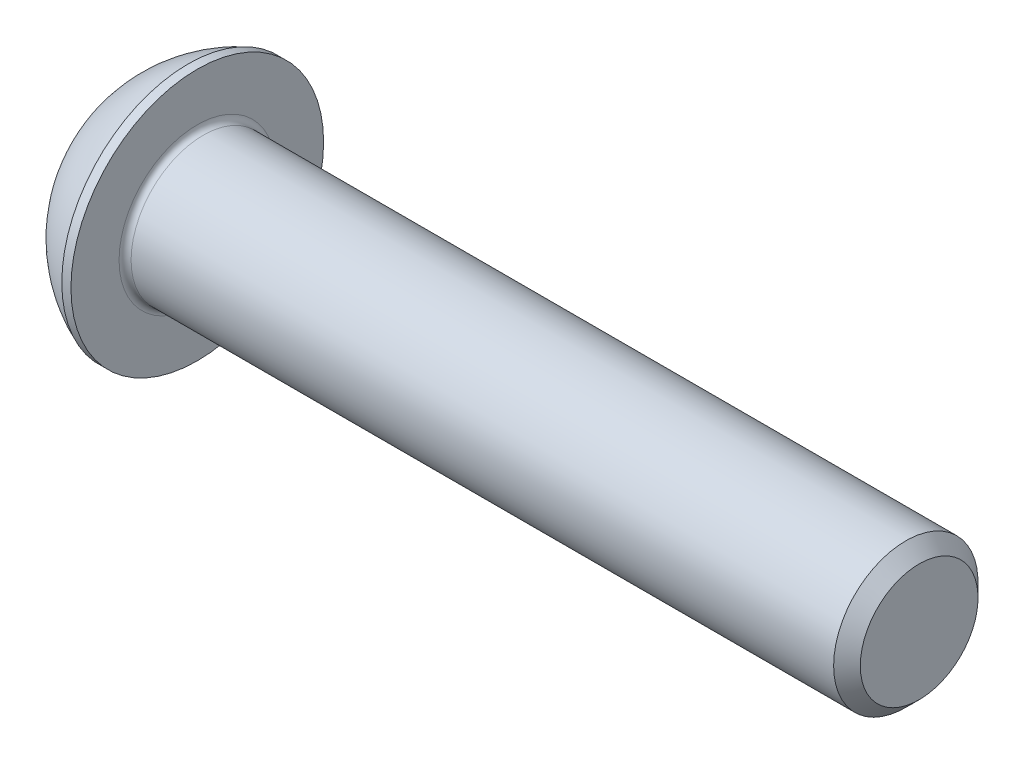
SolidWorks part; units mm, degrees
ref_plane "Plane1" through (0, 0, 0) normal (0, 0, 1) x (1, 0, 0)
ref_plane "Plane2" through (0, 0, 0) normal (0, 1, 0) x (1, 0, 0)
ref_plane "Plane3" through (0, 0, 0) normal (1, 0, 0) x (0, 0, -1)
sketch "BodySke" plane through (0, 0, 0) normal (0, 0, 1) x (1, 0, 0)
  line L0 (33.3, 0) -> (33.3, 2.4455)
  line L1 (32.7455, 3) -> (3.3, 3)
  line L2 (3.3, 3) -> (3.3, 5.25)
  line L3 (3.3, 5.25) -> (2.92, 5.25)
  line L4 (0, 0) -> (101.6, 0) construction
  line L5 (3.3, -5.25) -> (2.92, -5.25) construction
  line L6 (55.6768, -3) -> (3.3, -3) construction
  line L7 (33.3, 0) -> (0, 0)
  line L8 (0, 2.625) -> (0, -2.625) construction
  line L9 (0, 0) -> (0, 2.625)
  line L10 (33.3, 2.4455) -> (32.7455, 3)
  line L11 (33.3, -2.4455) -> (32.7455, -3) construction
  line L12 (4.3, 9.525) -> (4.3, -3) construction
  line L13 (3.3, 9.525) -> (3.3, -3) construction
  arc A1 (0, 2.625) -> (2.92, 5.25) centre (4.9997, 0) cw
  dimension "Head_side_ht" = 0.38
  dimension "Body_ch_ang" = 45
revolve "BaseBody" add sketch "BodySke" angle 360 about L4
cosmetic thread "ThreadCosmetic" [suppressed] parameters "Thread_length"=28, "Thread_minor"=4.891
fillet "Fillet1" radius 0.25 1 edges at (3.3, 0, 3)
sketch "Sketch2" plane through (0, 0, 0) normal (0, 0, 1) x (1, 0, 0)
  line L0 (0, 2) -> (2.08, 2)
  line L1 (2.08, 2) -> (3.2347, 0)
  line L3 (3.2347, 0) -> (0, 0)
  line L4 (0, 0) -> (0, 2)
  line L5 (0, -2) -> (2.08, -2) construction
  line L6 (0, 0) -> (47.625, 0) construction
  dimension "D2" = 60
  dimension "PreBroach_depth" = 2.08
  dimension "PreBroach_dia" = 4
revolve "PreBroach" cut sketch "Sketch2" angle 360 about L6
sketch "Sketch3" plane through (0, 0, 0) normal (1, 0, 0) x (0, 0, -1)
  line L0 (-2, -1.1547) -> (-2, 1.1547)
  line L1 (-2, 1.1547) -> (0, 2.3094)
  line L2 (0, 2.3094) -> (2, 1.1547)
  line L3 (2, 1.1547) -> (2, -1.1547)
  line L4 (2, -1.1547) -> (0, -2.3094)
  line L5 (0, -2.3094) -> (-2, -1.1547)
extrude "Hex" cut sketch "Sketch3" along normal blind 2.08
sketch "ThdSchSke" plane through (0, 0, 0) normal (0, 0, 1) x (1, 0, 0)
  line L0 (5.3, -2.4455) -> (4.9117, -3)
  line L1 (5.3, -2.4455) -> (5.6883, -3)
  line L2 (5.6883, -3) -> (5.6883, -3.75)
  line L3 (-3.175, 0) -> (5.1513, 0) construction
  line L5 (5.6883, -3.75) -> (4.9117, -3.75)
  line L6 (4.9117, -3.75) -> (4.9117, -3)
  dimension "SideAngle" = 55
  dimension "VeeAngle" = 70
revolve "ThreadSchematic" [suppressed] cut sketch "ThdSchSke" angle 360 about L3
pattern_linear "ThdSchPat" [suppressed]
equation "\"D1@BodySke\" = \"Head_dia@BodySke\" * .5"
equation "\"Thread_minor@ThreadCosmetic\" = \"Minor_dia@BodySke\""
equation "\"D1@Sketch3\" = \"Hex_size@Sketch3\" / 2"
equation "\"D2@Sketch3\" = \"D1@Sketch3\""
equation "\"D3@Sketch3\" = \"Hex_size@Sketch3\""
equation "\"Thread_length@ThreadCosmetic\" = ((sgn( (\"Length@BodySke\" - \"Advance@BodySke\" * 2.0) - \"Thread_nom@BodySke\" )-1)*( (\"Length@BodySke\" - \"Advance@BodySke\" * 2.0) - \"Thread_nom@BodySke\" ))/-2+ \"Thread_nom@BodySke\""
equation "\"Thread_minor@ThdSchSke\" = \"Minor_dia@BodySke\""
equation "\"Diameter@ThdSchSke\" = \"Diameter@BodySke\""
equation "\"Overcut@ThdSchSke\" = \"Diameter@BodySke\" * 1.25"
equation "\"Start@ThdSchSke\" = \"Head_ht@BodySke\" + \"Length@BodySke\" - \"Thread_length@ThreadCosmetic\"  '---Non-countersunk---"
equation "\"Num_threads@ThdSchPat\" = int( \"Thread_length@ThreadCosmetic\" / \"Advance@BodySke\" + 0.999 )  + 1"
equation "\"Advance@ThdSchPat\" = \"Thread_length@ThreadCosmetic\" /  (\"Num_threads@ThdSchPat\" - 1) 'relax it"
equation "\"Num_threads@ThdSchPat\" = \"Num_threads@ThdSchPat\" - sgn( \"Num_threads@ThdSchPat\" - 1) '---chamfered tips only---"
